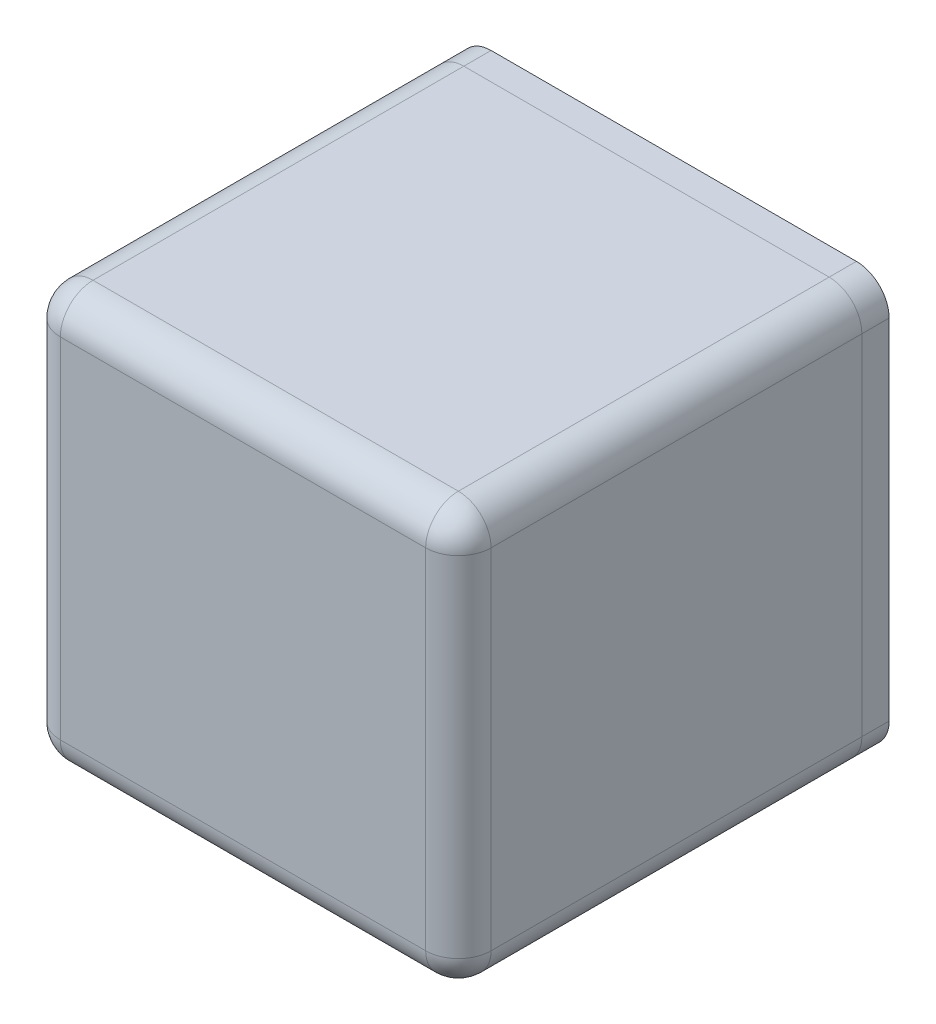
SolidWorks part; units mm, degrees
ref_plane "Front Plane" through (0, 0, 0) normal (0, 0, 1) x (1, 0, 0)
ref_plane "Top Plane" through (0, 0, 0) normal (0, 1, 0) x (1, 0, 0)
ref_plane "Right Plane" through (0, 0, 0) normal (1, 0, 0) x (0, 0, -1)
sketch "Sketch3" plane through (0, 0, 0) normal (1, 0, 0) x (0, 0, -1)
  line L1 (-18.5, 19) -> (18.5, 19)
  line L2 (-18.5, 19) -> (-18.5, -19)
  line L3 (-18.5, -19) -> (18.5, -19)
  line L4 (18.5, 19) -> (18.5, -19)
  line L5 (-18.5, 19) -> (18.5, -19) construction
  line L6 (-18.5, -19) -> (18.5, 19) construction
  point P0 (0, 0)
  dimension "D1" = 38
  dimension "D2" = 37
extrude "Boss-Extrude3" add sketch "Sketch3" along normal mid plane 39.5 separate body
fillet "Fillet1" radius 3 8 edges at (19.75, 19, 0) (19.75, 0, 18.5) (0, 19, 18.5) (-19.75, 0, 18.5) (-19.75, 19, 0) (0, -19, 18.5) (-19.75, -19, 0) (19.75, -19, 0)
shell "Shell2" thickness 2
sketch "Sketch6" plane through (0, 0, -18.5) normal (0, 0, -1) x (-1, 0, 0)
  line L0 (0, 0) -> (0, 7.5777) construction
  line L1 (0, 0) -> (-5.9833, 0) construction
  line L2 (-13.5, 15.5) -> (-13.5, 18.25)
  line L5 (-13.5, 18.25) -> (-16.25, 18.25)
  line L6 (-19, 15.5) -> (-19, 12.75)
  line L7 (-19, 12.75) -> (-16.25, 12.75)
  line L8 (-19, -12.75) -> (-16.25, -12.75)
  line L9 (-19, -15.5) -> (-19, -12.75)
  line L10 (-13.5, -18.25) -> (-16.25, -18.25)
  line L11 (-13.5, -15.5) -> (-13.5, -18.25)
  line L12 (13.5, -15.5) -> (13.5, -18.25)
  line L13 (13.5, -18.25) -> (16.25, -18.25)
  line L14 (19, -15.5) -> (19, -12.75)
  line L15 (19, -12.75) -> (16.25, -12.75)
  line L16 (19, 12.75) -> (16.25, 12.75)
  line L17 (19, 15.5) -> (19, 12.75)
  line L18 (13.5, 18.25) -> (16.25, 18.25)
  line L19 (13.5, 15.5) -> (13.5, 18.25)
  line L20 (-16.75, 17) -> (16.75, 17) construction
  line L21 (-17.75, -16) -> (-17.75, 16) construction
  circle A0 centre (-16.25, 15.5) radius 1.25
  arc A1 (-16.25, 12.75) -> (-13.5, 15.5) centre (-16.25, 15.5) ccw
  arc A2 (-16.25, -18.25) -> (-19, -15.5) centre (-16.25, -15.5) cw
  arc A3 (-16.25, 18.25) -> (-19, 15.5) centre (-16.25, 15.5) ccw
  arc A10 (-16.25, -12.75) -> (-13.5, -15.5) centre (-16.25, -15.5) cw
  circle A11 centre (-16.25, -15.5) radius 1.25
  circle A12 centre (16.25, -15.5) radius 1.25
  arc A13 (16.25, -12.75) -> (13.5, -15.5) centre (16.25, -15.5) ccw
  arc A14 (16.25, 18.25) -> (19, 15.5) centre (16.25, 15.5) cw
  arc A15 (16.25, -18.25) -> (19, -15.5) centre (16.25, -15.5) ccw
  arc A16 (16.25, 12.75) -> (13.5, 15.5) centre (16.25, 15.5) cw
  circle A17 centre (16.25, 15.5) radius 1.25
  dimension "D1" = 2.5
  dimension "D2" = 1.5
  dimension "D3" = 1.5
  dimension "D4" = 1.5
extrude "Boss-Extrude5" add sketch "Sketch6" against normal up to next
sketch "Sketch8" plane through (0, 0, 16.5) normal (0, 0, -1) x (-1, 0, 0)
  line L0 (10.75, 9.5248) -> (10.75, 3.6248) construction
  line L5 (10.75, 17) -> (13.5, 17)
  line L6 (10.75, 17) -> (10.75, 9.5248)
  line L7 (10.75, 9.5248) -> (17.75, 9.5248)
  line L8 (17.75, 12.75) -> (17.75, 9.5248)
  line L9 (17.75, 3.6248) -> (10.75, 3.6248)
  line L10 (17.75, 3.6248) -> (17.75, -5.4752)
  line L12 (10.75, 3.6248) -> (10.75, -5.4752)
  line L13 (17.145, 3.8248) -> (-17.145, 3.8248) construction
  line L14 (13.5, -16) -> (13.5, -15.5) construction
  line L15 (13.5, -17) -> (13.5, -15.5)
  line L16 (0, 0) -> (7.1113, 0) construction
  line L20 (17.75, -5.4752) -> (10.75, -5.4752)
  line L22 (10.75, -11.3752) -> (17.75, -11.3752)
  line L23 (10.75, -17) -> (10.75, -11.3752)
  line L24 (10.75, -17) -> (13.5, -17)
  line L25 (16.25, 12.75) -> (17.75, 12.75) construction
  line L26 (17.75, -12.75) -> (17.75, 12.75) construction
  line L27 (10.75, -5.4752) -> (10.75, -11.3752) construction
  line L28 (-13.5, 17) -> (13.5, 17) construction
  line L29 (16.25, -12.75) -> (17.75, -12.75)
  line L31 (17.75, -12.75) -> (17.75, -11.3752)
  line L35 (13.5, 17) -> (13.5, 15.5) construction
  line L36 (16.25, 12.75) -> (17.75, 12.75)
  line L37 (13.5, 17) -> (13.5, 15.5)
  arc A4 (13.5, -15.5) -> (16.25, -12.75) centre (16.25, -15.5) cw
  arc A8 (13.5, 15.5) -> (16.25, 12.75) centre (16.25, 15.5) ccw construction
  arc A9 (13.5, 15.5) -> (16.25, 12.75) centre (16.25, 15.5) ccw
  dimension "D1" = 0.2
  dimension "D2" = 5.9
  dimension "D3" = 15
  dimension "D4" = 7
extrude "Boss-Extrude6" add sketch "Sketch8" along normal blind 8
sketch "Sketch4" plane through (-19.75, 0, 0) normal (1, 0, 0) x (0, 0, -1)
  line L0 (-4.9, 3.5248) -> (-4.9, 9.6248) construction
  line L1 (-4.7, 6.5748) -> (-16.5, 6.5748) construction
  line L2 (-16.5, 9.5248) -> (-16.5, 3.6248) construction
  line L5 (-5.7, -12.2752) -> (-14.6, -12.2752) construction
  line L6 (-15.4, -11.4752) -> (-15.4, -5.3752) construction
  line L7 (-14.6, -4.5752) -> (-5.7, -4.5752) construction
  line L8 (-4.9, -5.3752) -> (-4.9, -11.4752) construction
  line L9 (0, -0.9252) -> (-13.9496, -0.9252) construction
  line L10 (-14.6, 2.7248) -> (-5.7, 2.7248) construction
  line L11 (-15.4, 9.6248) -> (-15.4, 3.5248) construction
  line L12 (-5.7, 10.4248) -> (-14.6, 10.4248) construction
  line L17 (-5.7, 10.6248) -> (-14.6, 10.6248)
  line L18 (-15.6, 9.6248) -> (-15.6, 3.5248)
  line L19 (-14.6, 2.5248) -> (-5.7, 2.5248)
  line L20 (-4.7, 3.5248) -> (-4.7, 9.6248)
  line L21 (-14.6, -4.3752) -> (-5.7, -4.3752)
  line L22 (-4.7, -5.3752) -> (-4.7, -11.4752)
  line L23 (-5.7, -12.4752) -> (-14.6, -12.4752)
  line L24 (-15.6, -11.4752) -> (-15.6, -5.3752)
  line L25 (-18.5, 16) -> (-18.5, -16) construction
  arc A4 (-5.7, -12.2752) -> (-4.9, -11.4752) centre (-5.7, -11.4752) ccw construction
  arc A5 (-15.4, -11.4752) -> (-14.6, -12.2752) centre (-14.6, -11.4752) ccw construction
  arc A6 (-14.6, -4.5752) -> (-15.4, -5.3752) centre (-14.6, -5.3752) ccw construction
  arc A7 (-4.9, -5.3752) -> (-5.7, -4.5752) centre (-5.7, -5.3752) ccw construction
  arc A8 (-4.9, 3.5248) -> (-5.7, 2.7248) centre (-5.7, 3.5248) cw construction
  arc A9 (-14.6, 2.7248) -> (-15.4, 3.5248) centre (-14.6, 3.5248) cw construction
  arc A10 (-15.4, 9.6248) -> (-14.6, 10.4248) centre (-14.6, 9.6248) cw construction
  arc A11 (-5.7, 10.4248) -> (-4.9, 9.6248) centre (-5.7, 9.6248) cw construction
  arc A12 (-15.6, 9.6248) -> (-14.6, 10.6248) centre (-14.6, 9.6248) cw
  arc A13 (-14.6, 2.5248) -> (-15.6, 3.5248) centre (-14.6, 3.5248) cw
  arc A14 (-4.7, 3.5248) -> (-5.7, 2.5248) centre (-5.7, 3.5248) cw
  arc A15 (-5.7, 10.6248) -> (-4.7, 9.6248) centre (-5.7, 9.6248) cw
  arc A16 (-4.7, -5.3752) -> (-5.7, -4.3752) centre (-5.7, -5.3752) ccw
  arc A17 (-5.7, -12.4752) -> (-4.7, -11.4752) centre (-5.7, -11.4752) ccw
  arc A18 (-15.6, -11.4752) -> (-14.6, -12.4752) centre (-14.6, -11.4752) ccw
  arc A19 (-14.6, -4.3752) -> (-15.6, -5.3752) centre (-14.6, -5.3752) ccw
  dimension "D4" = 0.8
  dimension "D1" = 15
  dimension "D5" = 3.1
  dimension "D7" = 8.1
  dimension "D8" = 10.9
  dimension "D2" = 0.2
  dimension "D3" = 0.2
extrude "Cut-Extrude2" cut sketch "Sketch4" along normal blind 3
sketch "Sketch9" plane through (0, 0, -18.5) normal (0, 0, -1) x (-1, 0, 0)
  line L4 (16.75, 18) -> (-16.75, 18)
  line L7 (-18.75, 16) -> (-18.75, -16)
  line L14 (-16.75, -18) -> (16.75, -18)
  line L17 (18.75, -16) -> (18.75, 16)
  line L20 (-13.5, 17) -> (-13.5, 15.5)
  line L21 (13.5, 17) -> (-13.5, 17)
  line L22 (13.5, 15.5) -> (13.5, 17)
  line L23 (17.75, 12.75) -> (16.25, 12.75)
  line L24 (17.75, -12.75) -> (17.75, 12.75)
  line L25 (16.25, -12.75) -> (17.75, -12.75)
  line L26 (13.5, -17) -> (13.5, -15.5)
  line L27 (-13.5, -17) -> (13.5, -17)
  line L28 (-13.5, -15.5) -> (-13.5, -17)
  line L29 (-17.75, -12.75) -> (-16.25, -12.75)
  line L30 (-17.75, 12.75) -> (-17.75, -12.75)
  line L31 (-16.25, 12.75) -> (-17.75, 12.75)
  line L32 (-13.5, 17) -> (-13.5, 15.5)
  line L33 (13.5, 17) -> (-13.5, 17)
  line L34 (13.5, 15.5) -> (13.5, 17)
  line L35 (17.75, 12.75) -> (16.25, 12.75)
  line L36 (17.75, -12.75) -> (17.75, 12.75)
  line L37 (16.25, -12.75) -> (17.75, -12.75)
  line L38 (13.5, -17) -> (13.5, -15.5)
  line L39 (-13.5, -17) -> (13.5, -17)
  line L40 (-13.5, -15.5) -> (-13.5, -17)
  line L41 (-17.75, -12.75) -> (-16.25, -12.75)
  line L42 (-17.75, 12.75) -> (-17.75, -12.75)
  line L43 (-16.25, 12.75) -> (-17.75, 12.75)
  line L44 (-18.75, 13.75) -> (-18.75, -13.75) construction
  line L45 (-14.5, -18) -> (14.5, -18) construction
  line L46 (18.75, -13.75) -> (18.75, 13.75) construction
  line L47 (14.5, 18) -> (-14.5, 18) construction
  line L56 (-16.25, 13.75) -> (-18.75, 13.75) construction
  line L57 (-14.5, 18) -> (-14.5, 15.5) construction
  line L58 (14.5, 15.5) -> (14.5, 18) construction
  line L59 (18.75, 13.75) -> (16.25, 13.75) construction
  line L60 (14.5, -18) -> (14.5, -15.5) construction
  line L61 (16.25, -13.75) -> (18.75, -13.75) construction
  line L62 (-18.75, -13.75) -> (-16.25, -13.75) construction
  line L63 (-14.5, -15.5) -> (-14.5, -18) construction
  arc A8 (13.5, 15.5) -> (16.25, 12.75) centre (16.25, 15.5) ccw
  arc A9 (16.25, -12.75) -> (13.5, -15.5) centre (16.25, -15.5) ccw
  arc A10 (-13.5, -15.5) -> (-16.25, -12.75) centre (-16.25, -15.5) ccw
  arc A11 (-16.25, 12.75) -> (-13.5, 15.5) centre (-16.25, 15.5) ccw
  arc A12 (13.5, 15.5) -> (16.25, 12.75) centre (16.25, 15.5) ccw
  arc A13 (16.25, -12.75) -> (13.5, -15.5) centre (16.25, -15.5) ccw
  arc A14 (-13.5, -15.5) -> (-16.25, -12.75) centre (-16.25, -15.5) ccw
  arc A15 (-16.25, 12.75) -> (-13.5, 15.5) centre (-16.25, 15.5) ccw
  arc A16 (-18.75, -16) -> (-16.75, -18) centre (-16.75, -16) ccw
  arc A17 (16.75, -18) -> (18.75, -16) centre (16.75, -16) ccw
  arc A18 (18.75, 16) -> (16.75, 18) centre (16.75, 16) ccw
  arc A19 (-18.75, 16) -> (-16.75, 18) centre (-16.75, 16) cw
  circle A20 centre (-16.25, 15.5) radius 1.25 construction
  circle A21 centre (-16.25, 15.5) radius 1.25
  circle A22 centre (16.25, 15.5) radius 1.25 construction
  circle A23 centre (16.25, 15.5) radius 1.25
  arc A24 (-16.25, 13.75) -> (-14.5, 15.5) centre (-16.25, 15.5) ccw construction
  arc A25 (14.5, 15.5) -> (16.25, 13.75) centre (16.25, 15.5) ccw construction
  circle A26 centre (16.25, -15.5) radius 1.25 construction
  circle A27 centre (16.25, -15.5) radius 1.25
  arc A28 (16.25, -13.75) -> (14.5, -15.5) centre (16.25, -15.5) ccw construction
  circle A29 centre (-16.25, -15.5) radius 1.25 construction
  circle A30 centre (-16.25, -15.5) radius 1.25
  arc A31 (-14.5, -15.5) -> (-16.25, -13.75) centre (-16.25, -15.5) ccw construction
  dimension "D3" = 2
  dimension "D1" = 0
  dimension "D2" = 1
extrude "Boss-Extrude7" add sketch "Sketch9" along normal blind 1 draft 5
sketch "Sketch5" plane through (0, 0, -18.5) normal (0, 0, -1) x (-1, 0, 0)
  line L8 (19.75, -16) -> (19.75, 16)
  line L9 (16.75, 19) -> (-16.75, 19)
  line L10 (-19.75, 16) -> (-19.75, -16)
  line L11 (-16.75, -19) -> (16.75, -19)
  line L12 (19.75, -16) -> (19.75, 16)
  line L13 (16.75, 19) -> (-16.75, 19)
  line L14 (-19.75, 16) -> (-19.75, -16)
  line L15 (-16.75, -19) -> (16.75, -19)
  circle A0 centre (-16.25, 15.5) radius 1.3375 construction
  circle A1 centre (-16.25, 15.5) radius 1.3375
  arc A2 (19.75, 16) -> (16.75, 19) centre (16.75, 16) ccw
  arc A3 (-16.75, 19) -> (-19.75, 16) centre (-16.75, 16) ccw
  arc A4 (19.75, 16) -> (16.75, 19) centre (16.75, 16) ccw
  arc A5 (-16.75, 19) -> (-19.75, 16) centre (-16.75, 16) ccw
  circle A6 centre (16.25, 15.5) radius 1.3375 construction
  circle A7 centre (16.25, 15.5) radius 1.3375
  circle A8 centre (16.25, -15.5) radius 1.3375 construction
  circle A9 centre (16.25, -15.5) radius 1.3375
  circle A10 centre (-16.25, -15.5) radius 1.3375 construction
  circle A11 centre (-16.25, -15.5) radius 1.3375
  arc A16 (16.75, -19) -> (19.75, -16) centre (16.75, -16) ccw
  arc A17 (16.75, -19) -> (19.75, -16) centre (16.75, -16) ccw
  arc A18 (-19.75, -16) -> (-16.75, -19) centre (-16.75, -16) ccw
  arc A19 (-19.75, -16) -> (-16.75, -19) centre (-16.75, -16) ccw
  dimension "D1" = 0
extrude "Boss-Extrude4" add sketch "Sketch5" along normal blind 2.5 separate body
sketch "Sketch14" plane through (0, 0, -19.5) normal (0, 0, -1) x (-1, 0, 0)
  line L14 (17.6375, -12.6375) -> (17.6375, 12.6375)
  line L15 (17.6375, 12.6375) -> (16.25, 12.6375)
  line L16 (13.3875, 15.5) -> (13.3875, 16.8875)
  line L17 (13.3875, 16.8875) -> (-13.3875, 16.8875)
  line L18 (-13.3875, 16.8875) -> (-13.3875, 15.5)
  line L19 (-16.25, 12.6375) -> (-17.6375, 12.6375)
  line L20 (-17.6375, 12.6375) -> (-17.6375, -12.6375)
  line L21 (-17.6375, -12.6375) -> (-16.25, -12.6375)
  line L22 (-13.3875, -15.5) -> (-13.3875, -16.8875)
  line L23 (-13.3875, -16.8875) -> (13.3875, -16.8875)
  line L24 (13.3875, -16.8875) -> (13.3875, -15.5)
  line L25 (16.25, -12.6375) -> (17.6375, -12.6375)
  line L26 (-16.25, 12.8375) -> (-17.8375, 12.8375)
  line L27 (-13.5875, 17.0875) -> (-13.5875, 15.5)
  line L28 (13.5875, 17.0875) -> (-13.5875, 17.0875)
  line L29 (13.5875, 15.5) -> (13.5875, 17.0875)
  line L30 (17.8375, 12.8375) -> (16.25, 12.8375)
  line L31 (17.8375, -12.8375) -> (17.8375, 12.8375)
  line L32 (16.25, -12.8375) -> (17.8375, -12.8375)
  line L33 (13.5875, -17.0875) -> (13.5875, -15.5)
  line L34 (-13.5875, -17.0875) -> (13.5875, -17.0875)
  line L35 (-13.5875, -15.5) -> (-13.5875, -17.0875)
  line L36 (-17.8375, -12.8375) -> (-16.25, -12.8375)
  line L49 (-17.8375, 12.8375) -> (-17.8375, -12.8375)
  line L50 (-16.25, 12.8375) -> (-17.8375, 12.8375) construction
  line L51 (-13.5875, 17.0875) -> (-13.5875, 15.5) construction
  line L52 (13.5875, 17.0875) -> (-13.5875, 17.0875) construction
  line L53 (13.5875, 15.5) -> (13.5875, 17.0875) construction
  line L54 (17.8375, 12.8375) -> (16.25, 12.8375) construction
  line L55 (17.8375, -12.8375) -> (17.8375, 12.8375) construction
  line L56 (16.25, -12.8375) -> (17.8375, -12.8375) construction
  line L57 (13.5875, -17.0875) -> (13.5875, -15.5) construction
  line L58 (-13.5875, -17.0875) -> (13.5875, -17.0875) construction
  line L59 (-13.5875, -15.5) -> (-13.5875, -17.0875) construction
  line L60 (-17.8375, -12.8375) -> (-16.25, -12.8375) construction
  line L61 (-17.8375, 12.8375) -> (-17.8375, -12.8375) construction
  arc A5 (13.3875, 15.5) -> (16.25, 12.6375) centre (16.25, 15.5) ccw
  arc A6 (-16.25, 12.6375) -> (-13.3875, 15.5) centre (-16.25, 15.5) ccw
  arc A7 (-13.3875, -15.5) -> (-16.25, -12.6375) centre (-16.25, -15.5) ccw
  arc A8 (16.25, -12.6375) -> (13.3875, -15.5) centre (16.25, -15.5) ccw
  arc A9 (-16.25, 12.8375) -> (-13.5875, 15.5) centre (-16.25, 15.5) ccw
  arc A10 (13.5875, 15.5) -> (16.25, 12.8375) centre (16.25, 15.5) ccw
  arc A11 (16.25, -12.8375) -> (13.5875, -15.5) centre (16.25, -15.5) ccw
  arc A12 (-13.5875, -15.5) -> (-16.25, -12.8375) centre (-16.25, -15.5) ccw
  arc A17 (-16.25, 12.8375) -> (-13.5875, 15.5) centre (-16.25, 15.5) ccw construction
  arc A18 (13.5875, 15.5) -> (16.25, 12.8375) centre (16.25, 15.5) ccw construction
  arc A19 (16.25, -12.8375) -> (13.5875, -15.5) centre (16.25, -15.5) ccw construction
  arc A20 (-13.5875, -15.5) -> (-16.25, -12.8375) centre (-16.25, -15.5) ccw construction
  dimension "D1" = 0
  dimension "D2" = 0.2
extrude "Boss-Extrude8" add sketch "Sketch14" against normal blind 1.5 separate body
sketch "Sketch15" plane through (0, 0, -18.5) normal (0, 0, -1) x (-1, 0, 0)
  line L8 (-16.75, -18.1125) -> (16.75, -18.1125)
  line L9 (18.8625, -16) -> (18.8625, 16)
  line L10 (16.75, 18.1125) -> (-16.75, 18.1125)
  line L11 (-18.8625, 16) -> (-18.8625, -16)
  line L12 (-16.75, -18.1125) -> (16.75, -18.1125)
  line L13 (18.8625, -16) -> (18.8625, 16)
  line L14 (16.75, 18.1125) -> (-16.75, 18.1125)
  line L15 (-18.8625, 16) -> (-18.8625, -16)
  arc A8 (-18.8625, -16) -> (-16.75, -18.1125) centre (-16.75, -16) ccw
  arc A9 (16.75, -18.1125) -> (18.8625, -16) centre (16.75, -16) ccw
  arc A10 (18.8625, 16) -> (16.75, 18.1125) centre (16.75, 16) ccw
  arc A11 (-16.75, 18.1125) -> (-18.8625, 16) centre (-16.75, 16) ccw
  arc A12 (-18.8625, -16) -> (-16.75, -18.1125) centre (-16.75, -16) ccw
  arc A13 (16.75, -18.1125) -> (18.8625, -16) centre (16.75, -16) ccw
  arc A14 (18.8625, 16) -> (16.75, 18.1125) centre (16.75, 16) ccw
  arc A15 (-16.75, 18.1125) -> (-18.8625, 16) centre (-16.75, 16) ccw
  dimension "D1" = 0.2
extrude "Cut-Extrude3" cut sketch "Sketch15" along normal up to vertex (1 mm away) up to point (-16.75, 17.9125, -19.5)
combine bodies "Combine1" operation type add bodies to combine 129 130
sketch "Sketch16" plane through (0, 0, -18) normal (0, 0, 1) x (1, 0, 0)
  line L24 (-11.4262, -14.8875) -> (11.4262, -14.8875)
  line L25 (15.6375, -10.6762) -> (15.6375, 10.6762)
  line L26 (11.4262, 14.8875) -> (-11.4262, 14.8875)
  line L27 (-15.6375, 10.6762) -> (-15.6375, -10.6762)
  line L28 (-11.4262, -14.8875) -> (11.4262, -14.8875)
  line L29 (15.6375, -10.6762) -> (15.6375, 10.6762)
  line L30 (11.4262, 14.8875) -> (-11.4262, 14.8875)
  line L31 (-15.6375, 10.6762) -> (-15.6375, -10.6762)
  arc A8 (-11.4262, -14.8875) -> (-15.6375, -10.6762) centre (-16.25, -15.5) ccw
  arc A9 (15.6375, -10.6762) -> (11.4262, -14.8875) centre (16.25, -15.5) ccw
  arc A10 (11.4262, 14.8875) -> (15.6375, 10.6762) centre (16.25, 15.5) ccw
  arc A11 (-15.6375, 10.6762) -> (-11.4262, 14.8875) centre (-16.25, 15.5) ccw
  arc A12 (-11.4262, -14.8875) -> (-15.6375, -10.6762) centre (-16.25, -15.5) ccw
  arc A13 (15.6375, -10.6762) -> (11.4262, -14.8875) centre (16.25, -15.5) ccw
  arc A14 (11.4262, 14.8875) -> (15.6375, 10.6762) centre (16.25, 15.5) ccw
  arc A15 (-15.6375, 10.6762) -> (-11.4262, 14.8875) centre (-16.25, 15.5) ccw
  dimension "D1" = 2
extrude "Cut-Extrude4" cut sketch "Sketch16" against normal up to vertex (1.5 mm away) up to point (16.25, 12.6375, -19.5)
sketch "Sketch17" plane through (0, 0, -21) normal (0, 0, -1) x (-1, 0, 0)
  line L0 (-16.75, -19) -> (16.75, -19) construction
  line L1 (-12.75, 12) -> (2.25, 12)
  line L2 (-12.75, 12) -> (-12.75, -19)
  line L3 (-12.75, -19) -> (2.25, -19)
  line L4 (2.25, 12) -> (2.25, -19)
  line L5 (-19.75, 16) -> (-19.75, -16) construction
  dimension "D1" = 15
  dimension "D2" = 31
  dimension "D3" = 7
extrude "Cut-Extrude5" cut sketch "Sketch17" against normal up to next
